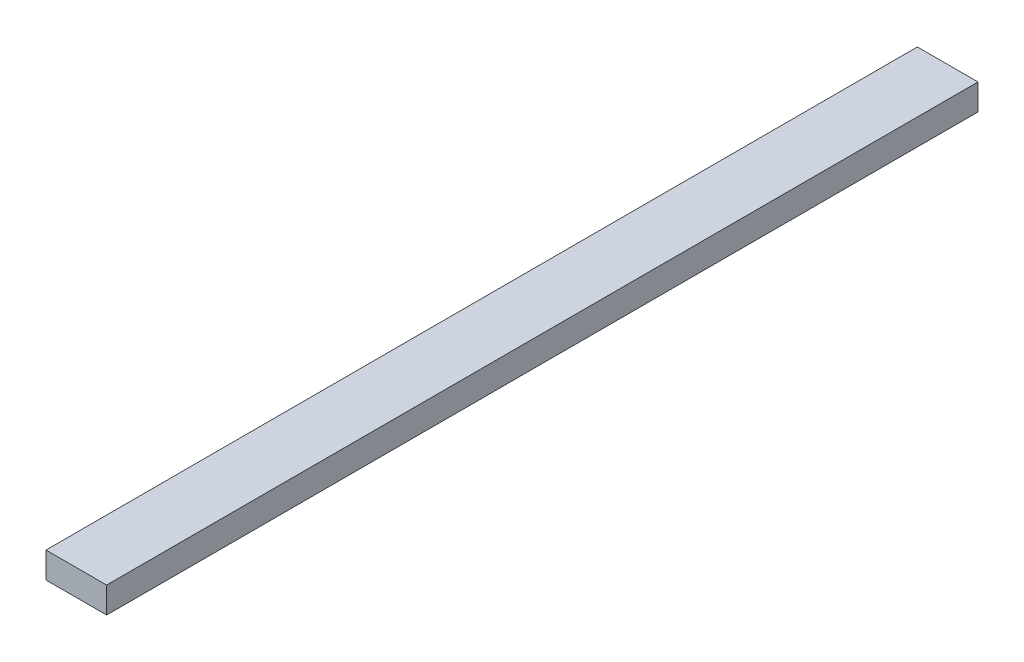
SolidWorks part; units mm, degrees
material "Pine"
ref_plane "Front Plane" through (0, 0, 0) normal (0, 0, 1) x (1, 0, 0)
ref_plane "Top Plane" through (0, 0, 0) normal (0, 1, 0) x (1, 0, 0)
ref_plane "Right Plane" through (0, 0, 0) normal (1, 0, 0) x (0, 0, -1)
sketch "Sketch1" plane through (0, 0, 0) normal (0, 0, 1) x (1, 0, 0)
  line L1 (44.45, 0) -> (44.45, -38.1)
  line L2 (44.45, -38.1) -> (-44.45, -38.1)
  line L3 (-44.45, -38.1) -> (-44.45, 0)
  line L4 (-44.45, 0) -> (44.45, 0)
  dimension "D1" = 38.1
  dimension "D2" = 88.9
extrude "Boss-Extrude1" add sketch "Sketch1" along normal mid plane 1277.8
equation "\"absorber_plate_width\" = 1100mm"
equation "\"absorber_plate_length\" = 2100mm"
equation "\"absorber_plate_thickness\" = .1875in"
equation "\"groove_depth\" = 20mm"
equation "\"frame_thickness\" = 60mm"
equation "\"insulation_thickness\" = 50mm"
equation "\"glass_thickness\" = 3mm"
equation "\"pipe_distances\" = 100mm"
equation "\"pipe_OD\" = 0.3125in"
equation "\"pipe_ID\" = 0.249in"
equation "\"pipe_straight_length\" = 900mm"
equation "\"absorber_to_glass\" = 25mm"
equation "\"serpentine_length\" = 1900mm"
equation "\"wood_width\" = 3.5in"
equation "\"wood_height\" = 1.5in"
equation "\"D2@Sketch1\"=\"wood_width\""
equation "\"D1@Boss-Extrude1\"=\"absorber_plate_width\"+\"wood_width\"*2"
